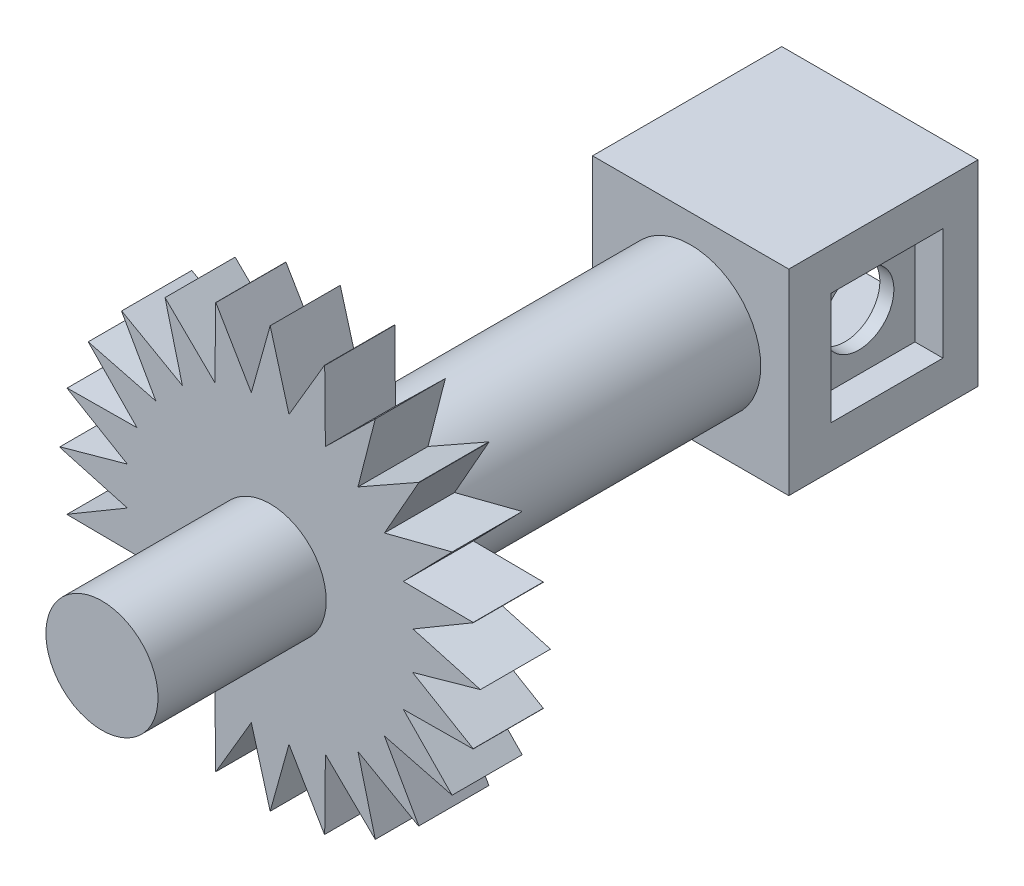
SolidWorks part; units mm, degrees
material "ABS"
ref_plane "Plan de face" through (0, 0, 0) normal (0, 0, 1) x (1, 0, 0)
ref_plane "Plan de dessus" through (0, 0, 0) normal (0, 1, 0) x (1, 0, 0)
ref_plane "Plan de droite" through (0, 0, 0) normal (1, 0, 0) x (0, 0, -1)
sketch "Esquisse1" plane through (0, 0, 0) normal (0, 0, 1) x (1, 0, 0)
  circle A0 centre (0, 0) radius 5
  dimension "D1" = 10
extrude "Boss.-Extru.2" add sketch "Esquisse1" along normal blind 70
sketch "Esquisse2" plane through (0, 0, 0) normal (0, 0, -1) x (-1, 0, 0)
  circle A0 centre (0, 0) radius 3.5
  dimension "D1" = 7
extrude "Boss.-Extru.3" add sketch "Esquisse2" along normal blind 12
sketch "Esquisse4" plane through (0, 0, 70) normal (0, 0, 1) x (1, 0, 0)
  circle A0 centre (0, 0) radius 15
  dimension "D1" = 30
extrude "Boss.-Extru.5" add sketch "Esquisse4" against normal blind 5
sketch "Esquisse5" plane through (0, 0, 70) normal (0, 0, 1) x (1, 0, 0)
  circle A0 centre (0, 0) radius 3.5
  dimension "D1" = 7
extrude "Boss.-Extru.6" add sketch "Esquisse5" along normal blind 12
sketch "Esquisse6" plane through (0, 0, 70) normal (0, 0, 1) x (1, 0, 0)
  line L0 (0, 10) -> (0, -10) construction
  line L1 (-10, 0) -> (10, 0) construction
  line L2 (0, 10) -> (0, 15) construction
  line L3 (10, 0) -> (15, 0) construction
  line L4 (15, 0) -> (-15, 0) construction
  line L5 (0, -10) -> (0, -15) construction
  line L6 (0, 15) -> (1.425, 9.8979)
  line L7 (0, 15) -> (-1.425, 9.8979)
  line L8 (0, 0) -> (-3.8907, 14.5215) construction
  line L9 (0, 0) -> (-7.5126, 13.022) construction
  line L10 (0, 0) -> (-10.6237, 10.6372) construction
  line L11 (0, 0) -> (-13.0125, 7.5291) construction
  line L12 (0, 0) -> (-14.5165, 3.9092) construction
  line L13 (-3.8907, 14.5215) -> (-1.1901, 9.9289)
  line L14 (-3.8907, 14.5215) -> (-3.9427, 9.19)
  line L15 (-7.4994, 12.9907) -> (-6.1827, 7.8596)
  line L16 (-7.4994, 12.9907) -> (-3.7145, 9.2845)
  line L17 (-14.5165, 3.9092) -> (-9.1849, 3.9543)
  line L18 (-14.5165, 3.9092) -> (-9.9274, 1.2028)
  line L19 (-10.6237, 10.6372) -> (-7.9997, 6.0004)
  line L20 (-10.6237, 10.6372) -> (-5.9821, 8.0134)
  line L21 (-12.9812, 7.516) -> (-7.8518, 6.1927)
  line L22 (-12.9812, 7.516) -> (-9.2798, 3.7263)
  line L23 (-15, 0.0191) -> (-9.8961, 1.4376)
  line L24 (-15, 0.0191) -> (-9.8998, -1.4124)
  line L25 (-15, -0.0191) -> (-9.8961, -1.4376)
  line L26 (-14.5165, -3.9092) -> (-9.9274, -1.2028)
  line L27 (-14.5165, -3.9092) -> (-9.1849, -3.9543)
  line L28 (-12.9812, -7.516) -> (-9.2798, -3.7263)
  line L29 (-12.9812, -7.516) -> (-7.8518, -6.1927)
  line L30 (-10.6237, -10.6372) -> (-7.9997, -6.0004)
  line L31 (-10.6237, -10.6372) -> (-5.9821, -8.0134)
  line L32 (-7.4994, -12.9907) -> (-6.1827, -7.8596)
  line L33 (-7.4994, -12.9907) -> (-3.7145, -9.2845)
  line L34 (-3.8907, -14.5215) -> (-3.9427, -9.19)
  line L35 (-3.8907, -14.5215) -> (-1.1901, -9.9289)
  line L36 (0, -15) -> (-1.425, -9.8979)
  line L37 (0, -15) -> (1.425, -9.8979)
  line L38 (3.8907, -14.5215) -> (1.1901, -9.9289)
  line L39 (3.8907, -14.5215) -> (3.9427, -9.19)
  line L40 (7.4994, -12.9907) -> (3.7145, -9.2845)
  line L41 (7.4994, -12.9907) -> (6.1827, -7.8596)
  line L42 (10.6237, -10.6372) -> (5.9821, -8.0134)
  line L43 (10.6237, -10.6372) -> (7.9997, -6.0004)
  line L44 (12.9812, -7.516) -> (7.8518, -6.1927)
  line L45 (12.9812, -7.516) -> (9.2798, -3.7263)
  line L46 (14.5165, -3.9092) -> (9.1849, -3.9543)
  line L47 (14.5165, -3.9092) -> (9.9274, -1.2028)
  line L48 (15, 0.0191) -> (9.8998, -1.4124)
  line L49 (15, 0.0191) -> (9.8961, 1.4376)
  line L50 (14.5165, 3.9092) -> (9.9274, 1.2028)
  line L51 (14.5165, 3.9092) -> (9.1849, 3.9543)
  line L52 (12.9812, 7.516) -> (9.2798, 3.7263)
  line L53 (12.9812, 7.516) -> (7.8518, 6.1927)
  line L54 (10.6237, 10.6372) -> (7.9997, 6.0004)
  line L55 (10.6237, 10.6372) -> (5.9821, 8.0134)
  line L56 (7.4994, 12.9907) -> (6.1827, 7.8596)
  line L57 (7.4994, 12.9907) -> (3.7145, 9.2845)
  line L58 (0, 15) -> (1.425, 9.8979)
  line L59 (3.8907, 14.5215) -> (3.9427, 9.19)
  line L60 (3.8907, 14.5215) -> (1.1901, 9.9289)
  circle A0 centre (0, 0) radius 10
  circle A1 centre (0, 0) radius 15 construction
  circle A2 centre (0, 0) radius 15.0337
  circle M35 centre (0, 0) radius 15
  dimension "D3" = 1.425
  dimension "D4" = 3.92
  dimension "D8" = 3.92
  dimension "D9" = 2.85
  dimension "D10" = 1.43
extrude "Enlèv. mat.-Extru.1" cut sketch "Esquisse6" against normal blind 12 contours L20 L15 M35 | L21 L19 M35 | L22 L17 M35 | L23 L18 M35 | L26 L25 M35 | L28 L27 M35 | L30 L29 M35 | L32 L31 M35 | L34 L33 M35 | L36 L35 M35 | L38 L37 M35 | L40 L39 M35 | L42 L41 M35 | L44 L43 M35 | L46 L45 M35 | L48 L47 M35 | L50 L49 M35 | L52 L51 M35 | L54 L53 M35 | L56 L55 M35 | L59 L57 M35 | L60 L6 M35 | L13 L7 M35 | L16 L14 M35
sketch "Esquisse7" plane through (0, 0, -12) normal (0, 0, -1) x (-1, 0, 0)
  circle A0 centre (0, 0) radius 5
extrude "Enlèv. mat.-Extru.2" cut sketch "Esquisse7" against normal blind 47
sketch "Esquisse8" plane through (0, 0, 35) normal (0, 0, -1) x (-1, 0, 0)
  line L1 (-7, -7) -> (7, -7)
  line L2 (-7, -7) -> (-7, 7)
  line L3 (-7, 7) -> (7, 7)
  line L4 (7, -7) -> (7, 7)
  line L5 (-7, -7) -> (7, 7) construction
  line L6 (-7, 7) -> (7, -7) construction
  point P0 (0, 0)
  dimension "D1" = 14
  dimension "D2" = 14
extrude "Boss.-Extru.7" add sketch "Esquisse8" against normal blind 5
sketch "Esquisse9" plane through (0, 0, 35) normal (0, 0, -1) x (-1, 0, 0)
  line L1 (-4, -4) -> (4, -4)
  line L2 (-4, -4) -> (-4, 4)
  line L3 (-4, 4) -> (4, 4)
  line L4 (4, -4) -> (4, 4)
  line L5 (-4, -4) -> (4, 4) construction
  line L6 (-4, 4) -> (4, -4) construction
  line L7 (-7, -7) -> (7, -7)
  line L8 (-7, -7) -> (-7, 7)
  line L9 (-7, 7) -> (7, 7)
  line L10 (7, -7) -> (7, 7)
  line L11 (-7, -7) -> (7, 7) construction
  line L12 (-7, 7) -> (7, -7) construction
  point P0 (0, 0)
  point P6 (0, 0)
  dimension "D1" = 8
  dimension "D2" = 8
extrude "Boss.-Extru.8" add sketch "Esquisse9" along normal blind 4.5
sketch "Esquisse10" plane through (0, 0, 35) normal (0, 0, -1) x (-1, 0, 0)
  line L1 (-4, -4) -> (4, -4)
  line L2 (-4, -4) -> (-4, 4)
  line L3 (-4, 4) -> (4, 4)
  line L4 (4, -4) -> (4, 4)
  line L5 (-4, -4) -> (4, 4) construction
  line L6 (-4, 4) -> (4, -4) construction
  point P0 (0, 0)
extrude "Enlèv. mat.-Extru.3" cut sketch "Esquisse10" against normal blind 3.5
sketch "Esquisse12" plane through (0, 0, 30.5) normal (0, 0, -1) x (-1, 0, 0)
  line L1 (-4, -4) -> (4, -4)
  line L2 (-4, -4) -> (-4, 4)
  line L3 (-4, 4) -> (4, 4)
  line L4 (4, -4) -> (4, 4)
  line L5 (-4, -4) -> (4, 4) construction
  line L6 (-4, 4) -> (4, -4) construction
  line L7 (-7, -7) -> (7, -7)
  line L8 (-7, -7) -> (-7, 7)
  line L9 (-7, 7) -> (7, 7)
  line L10 (7, -7) -> (7, 7)
  line L11 (-7, -7) -> (7, 7) construction
  line L12 (-7, 7) -> (7, -7) construction
  point P0 (0, 0)
  point P7 (0, 0)
extrude "Boss.-Extru.9" add sketch "Esquisse12" along normal blind 4
sketch "Esquisse14" plane through (-7, 0, 0) normal (-1, 0, 0) x (0, 0, 1)
  line L0 (40, -7) -> (40, 7) construction
  line L1 (37, 4) -> (29, 4)
  line L2 (37, 4) -> (37, -4)
  line L3 (37, -4) -> (29, -4)
  line L4 (29, 4) -> (29, -4)
  line L5 (37, 4) -> (29, -4) construction
  line L6 (37, -4) -> (29, 4) construction
  line L7 (40, -7) -> (26.5, -7) construction
  point P0 (33, 0)
  dimension "D1" = 8
  dimension "D2" = 8
  dimension "D3" = 3
  dimension "D4" = 3
extrude "Enlèv. mat.-Extru.4" cut sketch "Esquisse14" against normal blind 2
sketch "Esquisse15" plane through (-5, 0, 0) normal (-1, 0, 0) x (0, 0, 1)
  line L0 (29, -4) -> (37, -4) construction
  line L1 (29, 4) -> (29, -4) construction
  circle A0 centre (33, 0) radius 2.5
  dimension "D1" = 5
  dimension "D2" = 4
  dimension "D3" = 4
extrude "Enlèv. mat.-Extru.5" cut sketch "Esquisse15" against normal blind 2
sketch "Esquisse16" plane through (7, 0, 0) normal (1, 0, 0) x (0, 0, -1)
  line L0 (-40, 7) -> (-40, -7) construction
  line L1 (-29, -4) -> (-37, -4)
  line L2 (-29, -4) -> (-29, 4)
  line L3 (-29, 4) -> (-37, 4)
  line L4 (-37, -4) -> (-37, 4)
  line L5 (-29, -4) -> (-37, 4) construction
  line L6 (-29, 4) -> (-37, -4) construction
  line L7 (-40, -7) -> (-26.5, -7) construction
  point P0 (-33, 0)
  dimension "D1" = 8
  dimension "D2" = 8
  dimension "D3" = 3
  dimension "D4" = 3
extrude "Enlèv. mat.-Extru.6" cut sketch "Esquisse16" against normal blind 2
sketch "Esquisse17" plane through (5, 0, 0) normal (1, 0, 0) x (0, 0, -1)
  line L0 (-29, -4) -> (-29, 4) construction
  circle A0 centre (-33, 0) radius 2.5
  dimension "D1" = 5
  dimension "D2" = 4
extrude "Enlèv. mat.-Extru.7" cut sketch "Esquisse17" against normal blind 2
sketch "Esquisse18" plane through (0, 0, 82) normal (0, 0, 1) x (1, 0, 0)
  circle A0 centre (0, 0) radius 4
  dimension "D1" = 8
extrude "Boss.-Extru.10" add sketch "Esquisse18" against normal blind 12
